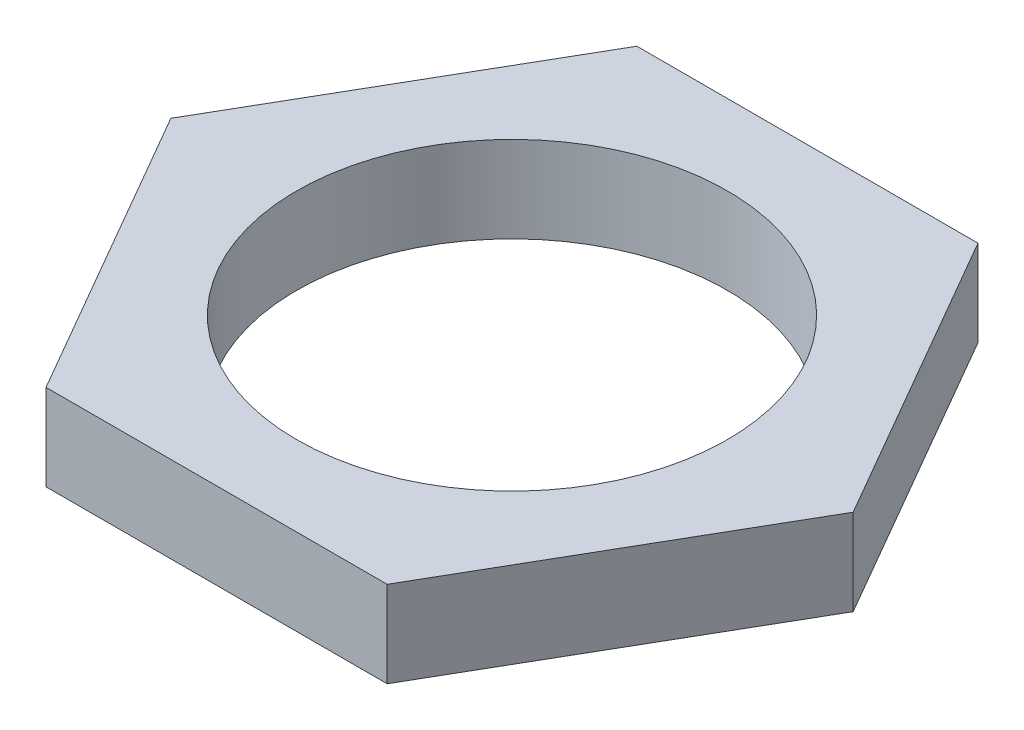
SolidWorks part; units mm, degrees
ref_plane "Front Plane" through (0, 0, 0) normal (0, 0, 1) x (1, 0, 0)
ref_plane "Top Plane" through (0, 0, 0) normal (0, 1, 0) x (1, 0, 0)
ref_plane "Right Plane" through (0, 0, 0) normal (1, 0, 0) x (0, 0, -1)
sketch "Sketch3" plane through (0, 0, 0) normal (0, 1, 0) x (1, 0, 0)
  line L1 (-6.9282, -12) -> (6.9282, -12)
  line L2 (6.9282, -12) -> (13.8564, 0)
  line L3 (13.8564, 0) -> (6.9282, 12)
  line L4 (6.9282, 12) -> (-6.9282, 12)
  line L5 (-6.9282, 12) -> (-13.8564, 0)
  line L6 (-13.8564, 0) -> (-6.9282, -12)
  circle A0 centre (0, 0) radius 12 construction
  circle A1 centre (0, 0) radius 8.75
  dimension "D2" = 17.5
  dimension "D1" = 24
extrude "Boss-Extrude2" add sketch "Sketch3" along normal blind 3.5
